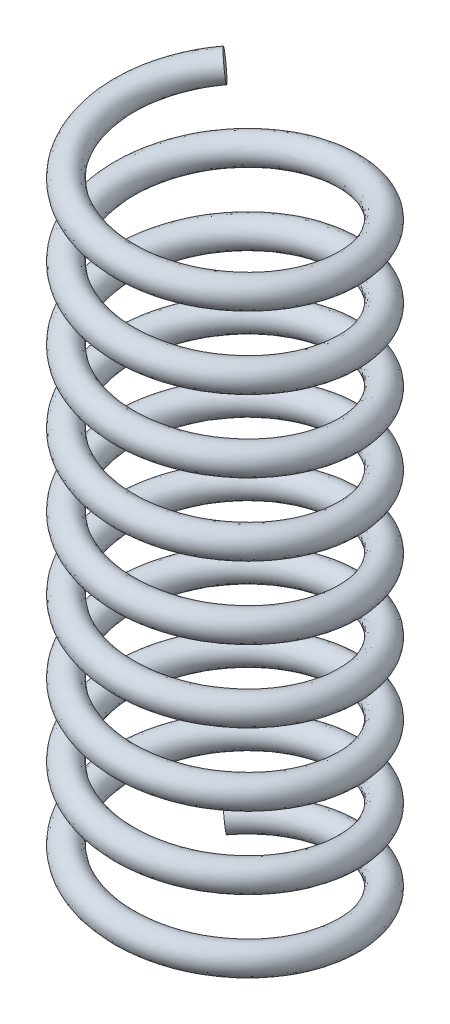
SolidWorks part; units mm, degrees
ref_plane "前视基准面" through (0, 0, 0) normal (0, 0, 1) x (1, 0, 0)
ref_plane "上视基准面" through (0, 0, 0) normal (0, 1, 0) x (1, 0, 0)
ref_plane "右视基准面" through (0, 0, 0) normal (1, 0, 0) x (0, 0, -1)
sketch "草图1" plane through (0, 0, 0) normal (0, 1, 0) x (1, 0, 0)
  circle A0 centre (0, 0) radius 2.65
  dimension "D1" = 5.3
curve "螺旋线/涡状线1" pitch 1.7 height 15.3 turns 9
ref_plane "基准面1" through (-1.8738, 0, -1.8738) normal (0.7034, 0.1016, -0.7034) x (-0.7107, 0.1005, -0.6962)
ref_plane "基准面2" through (0, -0.5, 0) normal (0, 1, 0) x (1, 0, 0)
sketch "草图2" plane through (-1.8738, 0, -1.8738) normal (0.7034, 0.1016, -0.7034) x (-0.7107, 0.1005, -0.6962)
  circle A0 centre (0, 0.0037) radius 0.325
  dimension "D1" = 0.65
sweep "扫描1" add profiles "草图2" path "螺旋线/涡状线1"
sketch "草图3" plane through (0, -0.5, 0) normal (0, 1, 0) x (1, 0, 0)
  circle A0 centre (0, 0) radius 5.0479
